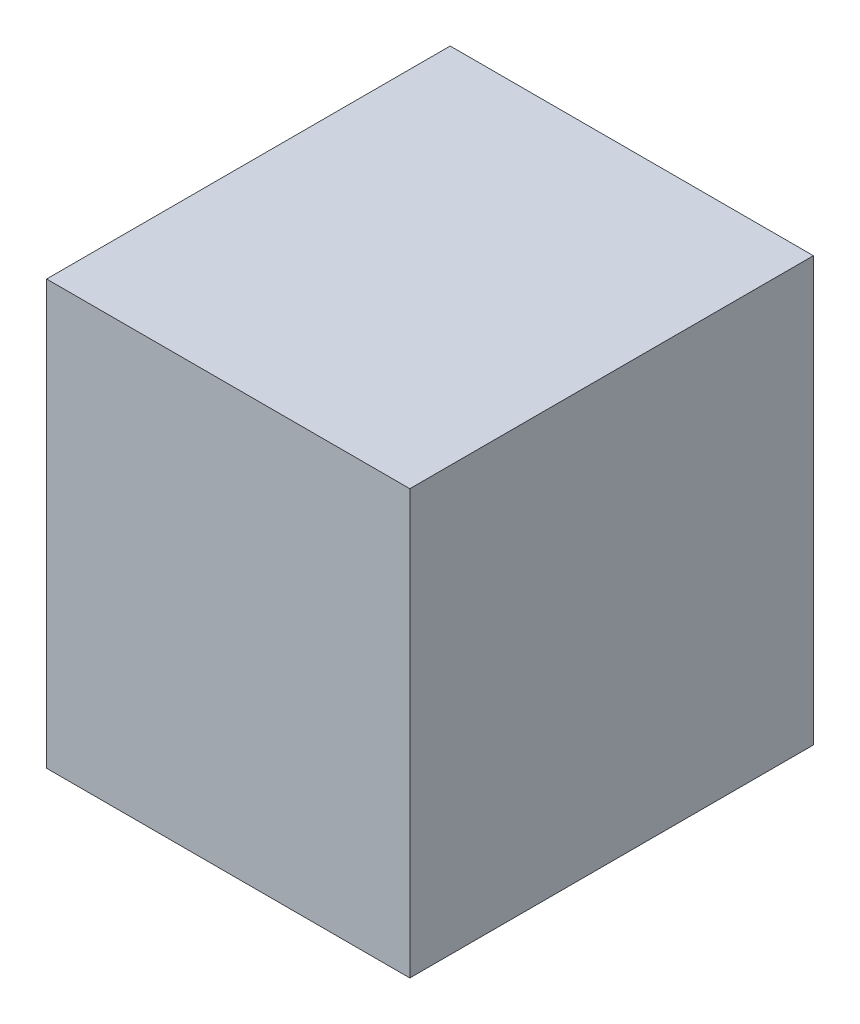
SolidWorks part; units mm, degrees
ref_plane "Front Plane" through (0, 0, 0) normal (0, 0, 1) x (1, 0, 0)
ref_plane "Top Plane" through (0, 0, 0) normal (0, 1, 0) x (1, 0, 0)
ref_plane "Right Plane" through (0, 0, 0) normal (1, 0, 0) x (0, 0, -1)
sketch "Sketch1" plane through (0, 0, 0) normal (0, 1, 0) x (1, 0, 0)
  line L1 (-155.448, 41.148) -> (73.152, 41.148)
  line L2 (-155.448, 41.148) -> (-155.448, -212.852)
  line L3 (-155.448, -212.852) -> (73.152, -212.852)
  line L4 (73.152, 41.148) -> (73.152, -212.852)
  dimension "D1" = 228.6
  dimension "D2" = 254
extrude "Boss-Extrude1" add sketch "Sketch1" along normal blind 266.7
